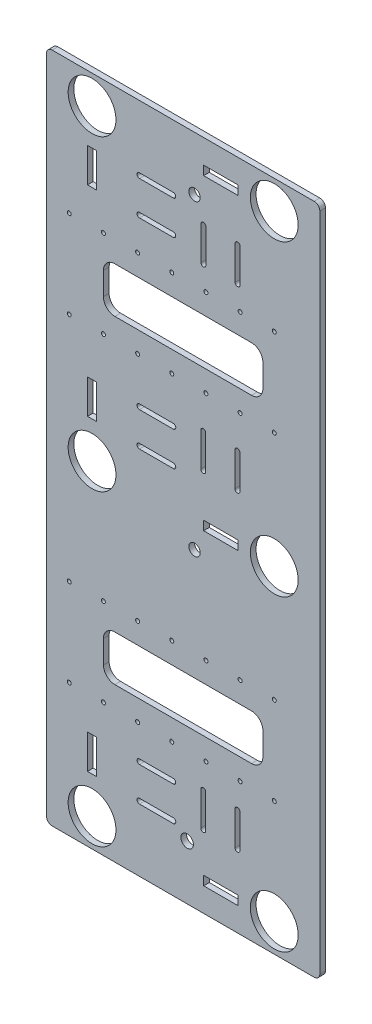
SolidWorks part; units mm, degrees
ref_plane "前视基准面" through (0, 0, 0) normal (0, 0, 1) x (1, 0, 0)
ref_plane "上视基准面" through (0, 0, 0) normal (0, 1, 0) x (1, 0, 0)
ref_plane "右视基准面" through (0, 0, 0) normal (1, 0, 0) x (0, 0, -1)
sketch "草图1" plane through (0, 0, 0) normal (0, 0, 1) x (1, 0, 0)
  line L0 (110.1165, 367.5) -> (-129.8835, 367.5) construction
  line L1 (110.1165, -197.5) -> (-129.8835, -197.5)
  line L2 (110.1165, -197.5) -> (110.1165, 392.5)
  line L3 (110.1165, 392.5) -> (-129.8835, 392.5)
  line L4 (-129.8835, -197.5) -> (-129.8835, 392.5)
  line L5 (-9.8835, 392.5) -> (-9.8835, -197.5) construction
  line L6 (110.1165, 97.5) -> (-129.8835, 97.5) construction
  line L7 (110.1165, -172.5) -> (-129.8835, -172.5) construction
  line L8 (-48.2335, 335.3298) -> (-18.5335, 335.3298) construction
  line L9 (70.1165, 367.5) -> (70.1165, -172.5) construction
  line L10 (-48.2335, 337.472) -> (-18.5335, 337.472)
  line L11 (-87.3835, 350) -> (-92.3835, 350) construction
  line L12 (-87.3835, 350) -> (-87.3835, 385) construction
  line L13 (-87.3835, 385) -> (-92.3835, 385) construction
  line L14 (-92.3835, 350) -> (-92.3835, 385) construction
  line L15 (-89.8835, 385) -> (-89.8835, 350) construction
  line L16 (-87.3835, 367.5) -> (-92.3835, 367.5) construction
  line L17 (-72.3835, 365) -> (-107.3835, 365) construction
  line L18 (-72.3835, 365) -> (-72.3835, 370) construction
  line L19 (-72.3835, 370) -> (-107.3835, 370) construction
  line L20 (-107.3835, 365) -> (-107.3835, 370) construction
  line L21 (-89.8835, 370) -> (-89.8835, 365) construction
  line L22 (-72.3835, 367.5) -> (-107.3835, 367.5) construction
  line L23 (-48.2335, 333.1877) -> (-18.5335, 333.1877)
  line L24 (-48.2335, 305.3298) -> (-18.5335, 305.3298) construction
  line L25 (-48.2335, 307.4554) -> (-18.5335, 307.4554)
  line L26 (5.6304, -104.15) -> (5.6304, -133.85) construction
  line L27 (9.9304, -133.85) -> (9.9304, -104.15) construction
  line L28 (35.6304, -104.15) -> (35.6304, -133.85) construction
  line L29 (39.9304, -133.85) -> (39.9304, -104.15) construction
  line L30 (-48.2335, 303.2042) -> (-18.5335, 303.2042)
  line L31 (7.8874, 325.85) -> (7.8874, 296.15) construction
  line L32 (10.0163, 325.85) -> (10.0163, 296.15)
  line L33 (5.7585, 325.85) -> (5.7585, 296.15)
  line L34 (37.8874, 325.85) -> (37.8874, 296.15) construction
  line L35 (40.0457, 325.85) -> (40.0457, 296.15)
  line L36 (35.7291, 325.85) -> (35.7291, 296.15)
  line L37 (-48.2335, 159.6169) -> (-18.5335, 159.6169) construction
  line L38 (-48.2335, 161.8047) -> (-18.5335, 161.8047)
  line L39 (-48.2335, 157.429) -> (-18.5335, 157.429)
  line L40 (-48.2335, 129.6169) -> (-18.5335, 129.6169) construction
  line L41 (-48.2335, 131.7815) -> (-18.5335, 131.7815)
  line L42 (-48.2335, 127.4523) -> (-18.5335, 127.4523)
  line L43 (7.7804, 168.85) -> (7.7804, 139.15) construction
  line L44 (9.9507, 168.85) -> (9.9507, 139.15)
  line L45 (5.6101, 168.85) -> (5.6101, 139.15)
  line L46 (37.7804, 168.85) -> (37.7804, 139.15) construction
  line L47 (39.9492, 168.85) -> (39.9492, 139.15)
  line L48 (35.6116, 168.85) -> (35.6116, 139.15)
  line L49 (-48.2335, -110.2834) -> (-18.5335, -110.2834) construction
  line L50 (5.6304, -104.15) -> (5.6304, -133.85)
  line L51 (9.9304, -133.85) -> (9.9304, -104.15)
  line L52 (35.6304, -104.15) -> (35.6304, -133.85)
  line L53 (39.9304, -133.85) -> (39.9304, -104.15)
  line L54 (-48.2335, -108.1626) -> (-18.5335, -108.1626)
  line L55 (-48.2335, -112.4042) -> (-18.5335, -112.4042)
  line L56 (-48.2335, -140.2834) -> (-18.5335, -140.2834) construction
  line L57 (-48.2335, -138.0793) -> (-18.5335, -138.0793)
  line L58 (-48.2335, -142.4875) -> (-18.5335, -142.4875)
  line L59 (-93.8835, 159.5) -> (-85.8835, 159.5)
  line L60 (-85.8835, 159.5) -> (-85.8835, 129.5)
  line L61 (-93.8835, 129.5) -> (-93.8835, 159.5)
  line L62 (-85.8835, 129.5) -> (-93.8835, 129.5)
  line L63 (8.1165, 93.5) -> (8.1165, 101.5)
  line L64 (8.1165, 101.5) -> (38.1165, 101.5)
  line L65 (38.1165, 93.5) -> (38.1165, 101.5)
  line L66 (38.1165, 93.5) -> (8.1165, 93.5)
  line L67 (-85.8835, 335.5) -> (-93.8835, 335.5)
  line L68 (-85.8835, 305.5) -> (-85.8835, 335.5)
  line L69 (-93.8835, 305.5) -> (-85.8835, 305.5)
  line L70 (-85.8835, -140.5) -> (-93.8835, -140.5)
  line L71 (-93.8835, -140.5) -> (-93.8835, -110.5)
  line L72 (-93.8835, -110.5) -> (-85.8835, -110.5)
  line L73 (-85.8835, -110.5) -> (-85.8835, -140.5)
  line L74 (38.1165, -176.5) -> (38.1165, -168.5)
  line L75 (38.1165, -176.5) -> (8.1165, -176.5)
  line L76 (8.1165, -176.5) -> (8.1165, -168.5)
  line L77 (8.1165, -168.5) -> (38.1165, -168.5)
  line L78 (-93.8835, 335.5) -> (-93.8835, 305.5)
  line L79 (38.1165, 371.5) -> (8.1165, 371.5)
  line L80 (8.1165, 371.5) -> (8.1165, 363.5)
  line L81 (8.1165, 363.5) -> (38.1165, 363.5)
  line L82 (38.1165, 371.5) -> (38.1165, 363.5)
  line L83 (-89.8835, -131.466) -> (-89.8835, -172.5) construction
  line L84 (60.1165, -32.5) -> (60.1165, -52.5)
  line L85 (50.1165, 217.5) -> (-69.8835, 217.5)
  line L86 (60.1165, 227.5) -> (60.1165, 247.5)
  line L87 (50.1165, 257.5) -> (-69.8835, 257.5)
  line L88 (-79.8835, 227.5) -> (-79.8835, 247.5)
  line L89 (-9.8835, 257.5) -> (-9.8835, 217.5) construction
  line L90 (60.1165, 237.5) -> (-79.8835, 237.5) construction
  line L91 (50.1165, -22.5) -> (-69.8835, -22.5)
  line L92 (-79.8835, -32.5) -> (-79.8835, -52.5)
  line L93 (50.1165, -62.5) -> (-69.8835, -62.5)
  circle A0 centre (-89.8835, 367.5) radius 17.6777 construction
  circle A1 centre (70.1165, 367.5) radius 17.6777 construction
  circle A2 centre (-89.8835, 97.5) radius 17.6777 construction
  circle A3 centre (-89.8835, -172.5) radius 17.6777 construction
  circle A4 centre (70.1165, -172.5) radius 17.6777 construction
  circle A5 centre (70.1165, 97.5) radius 17.6777 construction
  circle A6 centre (70.1165, 367.5) radius 21
  circle A7 centre (70.1165, 97.5) radius 21
  circle A8 centre (70.1165, -172.5) radius 21
  circle A9 centre (-89.8835, 367.5) radius 21
  circle A10 centre (-89.8835, 97.5) radius 21
  circle A11 centre (-89.8835, -172.5) radius 21
  arc A12 (-48.2335, 337.472) -> (-48.2335, 333.1877) centre (-48.2335, 335.3298) ccw
  arc A13 (-18.5335, 333.1877) -> (-18.5335, 337.472) centre (-18.5335, 335.3298) ccw
  arc A14 (-48.2335, 307.4554) -> (-48.2335, 303.2042) centre (-48.2335, 305.3298) ccw
  arc A15 (-18.5335, 303.2042) -> (-18.5335, 307.4554) centre (-18.5335, 305.3298) ccw
  arc A16 (9.9304, -104.15) -> (5.6304, -104.15) centre (7.7804, -104.15) ccw construction
  arc A17 (5.6304, -133.85) -> (9.9304, -133.85) centre (7.7804, -133.85) ccw construction
  arc A18 (35.6304, -133.85) -> (39.9304, -133.85) centre (37.7804, -133.85) ccw construction
  arc A19 (39.9304, -104.15) -> (35.6304, -104.15) centre (37.7804, -104.15) ccw construction
  arc A20 (10.0163, 325.85) -> (5.7585, 325.85) centre (7.8874, 325.85) ccw
  arc A21 (5.7585, 296.15) -> (10.0163, 296.15) centre (7.8874, 296.15) ccw
  arc A22 (40.0457, 325.85) -> (35.7291, 325.85) centre (37.8874, 325.85) ccw
  arc A23 (35.7291, 296.15) -> (40.0457, 296.15) centre (37.8874, 296.15) ccw
  arc A24 (-48.2335, 161.8047) -> (-48.2335, 157.429) centre (-48.2335, 159.6169) ccw
  arc A25 (-18.5335, 157.429) -> (-18.5335, 161.8047) centre (-18.5335, 159.6169) ccw
  arc A26 (-48.2335, 131.7815) -> (-48.2335, 127.4523) centre (-48.2335, 129.6169) ccw
  arc A27 (-18.5335, 127.4523) -> (-18.5335, 131.7815) centre (-18.5335, 129.6169) ccw
  arc A28 (9.9507, 168.85) -> (5.6101, 168.85) centre (7.7804, 168.85) ccw
  arc A29 (5.6101, 139.15) -> (9.9507, 139.15) centre (7.7804, 139.15) ccw
  arc A30 (39.9492, 168.85) -> (35.6116, 168.85) centre (37.7804, 168.85) ccw
  arc A31 (35.6116, 139.15) -> (39.9492, 139.15) centre (37.7804, 139.15) ccw
  arc A32 (-48.2335, -108.1626) -> (-48.2335, -112.4042) centre (-48.2335, -110.2834) ccw
  arc A33 (-18.5335, -112.4042) -> (-18.5335, -108.1626) centre (-18.5335, -110.2834) ccw
  arc A34 (-48.2335, -138.0793) -> (-48.2335, -142.4875) centre (-48.2335, -140.2834) ccw
  arc A35 (-18.5335, -142.4875) -> (-18.5335, -138.0793) centre (-18.5335, -140.2834) ccw
  arc A36 (60.1165, 247.5) -> (50.1165, 257.5) centre (50.1165, 247.5) ccw
  arc A37 (50.1165, 217.5) -> (60.1165, 227.5) centre (50.1165, 227.5) ccw
  arc A38 (-69.8835, 217.5) -> (-79.8835, 227.5) centre (-69.8835, 227.5) cw
  arc A39 (-69.8835, 257.5) -> (-79.8835, 247.5) centre (-69.8835, 247.5) ccw
  arc A40 (9.9304, -104.15) -> (5.6304, -104.15) centre (7.7804, -104.15) ccw
  arc A41 (5.6304, -133.85) -> (9.9304, -133.85) centre (7.7804, -133.85) ccw
  arc A42 (35.6304, -133.85) -> (39.9304, -133.85) centre (37.7804, -133.85) ccw
  arc A43 (39.9304, -104.15) -> (35.6304, -104.15) centre (37.7804, -104.15) ccw
  arc A44 (50.1165, -22.5) -> (60.1165, -32.5) centre (50.1165, -32.5) cw
  arc A45 (-69.8835, -22.5) -> (-79.8835, -32.5) centre (-69.8835, -32.5) ccw
  arc A46 (-69.8835, -62.5) -> (-79.8835, -52.5) centre (-69.8835, -52.5) cw
  arc A47 (60.1165, -52.5) -> (50.1165, -62.5) centre (50.1165, -52.5) cw
  circle A48 centre (-109.8835, 275.9541) radius 1.75
  circle A49 centre (-79.8835, 275.9541) radius 1.75
  circle A50 centre (-49.8835, 275.9541) radius 1.75
  circle A51 centre (-19.8835, 275.9541) radius 1.75
  circle A52 centre (10.1165, 275.9541) radius 1.75
  circle A53 centre (40.1165, 275.9541) radius 1.75
  circle A54 centre (40.1165, 199.0459) radius 1.75
  circle A55 centre (10.1165, 199.0459) radius 1.75
  circle A56 centre (-19.8835, 199.0459) radius 1.75
  circle A57 centre (-49.8835, 199.0459) radius 1.75
  circle A58 centre (-109.8835, 199.0459) radius 1.75
  circle A59 centre (-79.8835, 199.0459) radius 1.75
  circle A60 centre (70.1165, 275.9541) radius 1.75
  circle A61 centre (70.1165, 199.0459) radius 1.75
  circle A62 centre (40.1165, -80.9541) radius 1.75
  circle A63 centre (10.1165, -80.9541) radius 1.75
  circle A64 centre (-19.8835, -80.9541) radius 1.75
  circle A65 centre (-49.8835, -80.9541) radius 1.75
  circle A66 centre (-79.8835, -80.9541) radius 1.75
  circle A67 centre (-109.8835, -80.9541) radius 1.75
  circle A68 centre (70.1165, -4.0459) radius 1.75
  circle A69 centre (-79.8835, -4.0459) radius 1.75
  circle A70 centre (-109.8835, -4.0459) radius 1.75
  circle A71 centre (-49.8835, -4.0459) radius 1.75
  circle A72 centre (-19.8835, -4.0459) radius 1.75
  circle A73 centre (10.1165, -4.0459) radius 1.75
  circle A74 centre (40.1165, -4.0459) radius 1.75
  circle A75 centre (70.1165, -80.9541) radius 1.75
  circle A76 centre (-9.8835, 367.5) radius 7.5 construction
  circle A77 centre (-9.8835, 97.5) radius 7.5 construction
  circle A78 centre (-9.8835, -172.5) radius 7.5 construction
  circle A79 centre (0.1217, 345.1377) radius 5
  circle A80 centre (0.1217, 75.1377) radius 5
  circle A81 centre (-6.3999, -149.6623) radius 5.5
  point P45 (-33.3835, 335.3298)
  point P50 (-33.3835, 305.3298)
  point P69 (7.8874, 311)
  point P76 (37.8874, 311)
  point P85 (-33.3835, 159.6169)
  point P92 (-33.3835, 129.6169)
  point P99 (7.7804, 154)
  point P106 (37.7804, 154)
  point P113 (-33.3835, -110.2834)
  point P120 (-53, -172.5)
  point P121 (-89.8835, -140.5)
  point P126 (38.1165, -172.5)
  point P131 (-33.3835, -140.2834)
  point P136 (38, 97.5)
  point P148 (38, 367.5)
  point P156 (38.1165, 367.5)
  point P162 (-9.8835, 237.5)
  point P175 (-79.8835, 217.5)
  point P178 (-79.8835, 257.5)
  dimension "D9" = 3
  dimension "D10" = 42
  dimension "D22" = 10
  dimension "D23" = 3.5
  dimension "D20" = 3.5
  dimension "D27" = 15
  dimension "D28" = 15
  dimension "D29" = 15
  dimension "D1" = 240
  dimension "D2" = 590
  dimension "D3" = 270
  dimension "D4" = 8
  dimension "D5" = 35
  dimension "D6" = 35
  dimension "D7" = 5
  dimension "D8" = 5
  dimension "D12" = 32
  dimension "D13" = 30
  dimension "D14" = 8
  dimension "D15" = 32
  dimension "D16" = 30
  dimension "D17" = 2
  dimension "D18" = 2
  dimension "D19" = 160
  dimension "D21" = 120
  dimension "D24" = 20
  dimension "D25" = 7
  dimension "D26" = 50
  dimension "D11" = 3
extrude "凸台-拉伸1" add sketch "草图1" along normal blind 5
fillet "圆角1" radius 5 4 edges at (110.1165, 392.5, 2.5) (110.1165, -197.5, 2.5) (-129.8835, -197.5, 2.5) (-129.8835, 392.5, 2.5)
ref_plane "基准面1" through (0, 0, 0) normal (-1, 0, 0) x (0, 0, 1)
